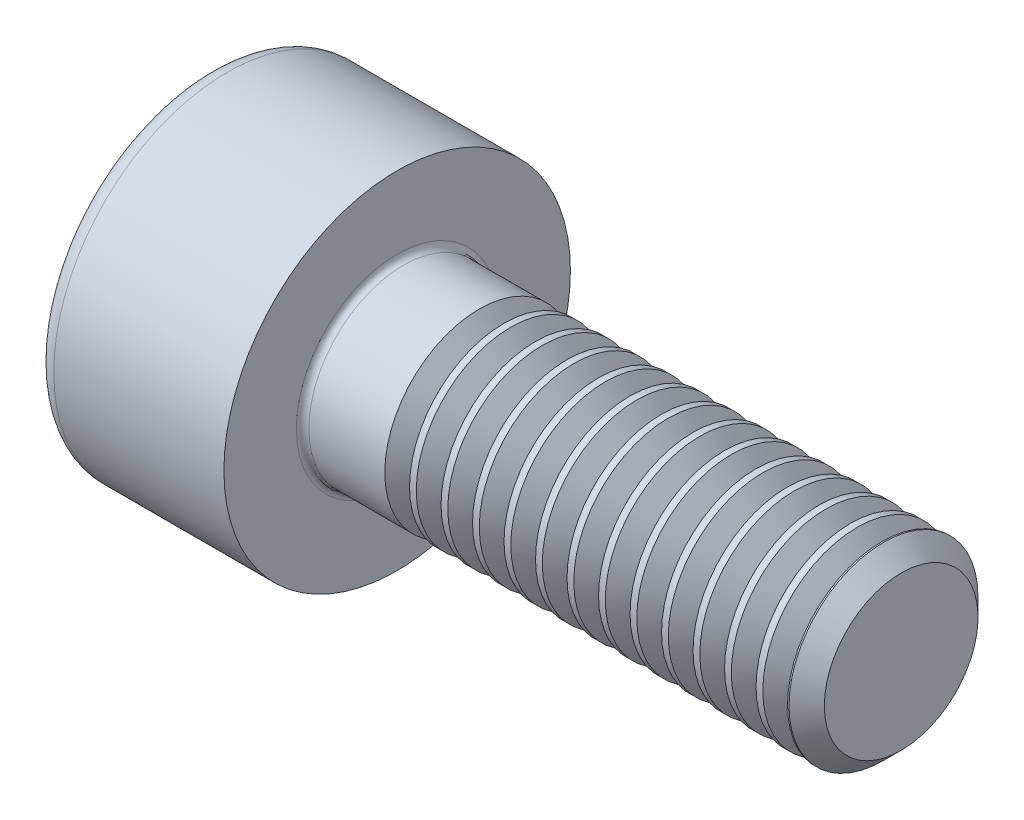
SolidWorks part; units mm, degrees
revolve "Base-Revolve" add sketch "BodySke"
sketch "BodySke" plane through (0, 0, 0) normal (0, 0, 1) x (1, 0, 0)
  line L0 (0, 0) -> (0, 2.75)
  line L1 (0, 2.75) -> (3, 2.75)
  line L2 (3, 2.75) -> (3, 1.5)
  line L3 (3, 1.5) -> (10.7195, 1.5)
  line L4 (11, 1.2195) -> (11, 0)
  line L5 (11, 0) -> (0, 0)
  line L6 (-31.75, 0) -> (127, 0) construction
  line L8 (11, 1.2195) -> (10.7195, 1.5)
  line L10 (11, -1.2195) -> (10.7195, -1.5) construction
  line L11 (3.5, 9.525) -> (3.5, 3.175) construction
  line L12 (3, 9.525) -> (3, 3.175) construction
  line L13 (3, 9.525) -> (3, 3.175) construction
cosmetic thread "ThreadCosmetic" [suppressed]
fillet "Fillet1" radius 0.1 1 edges at (3, 0, 1.5)
fillet "Fillet2" radius 0.3 1 edges at (0, 0, 2.75)
ref_plane "Plane1" through (0, 0, 0) normal (0, 0, 1) x (1, 0, 0)
ref_plane "Plane2" through (0, 0, 0) normal (0, 1, 0) x (1, 0, 0)
ref_plane "Plane3" through (0, 0, 0) normal (1, 0, 0) x (0, 0, -1)
sketch "Sketch2" plane through (0, 0, 0) normal (0, 0, 1) x (1, 0, 0)
  line L0 (0, 1.26) -> (1.3, 1.26)
  line L1 (1.3, 1.26) -> (2.0275, 0)
  line L2 (-31.75, 0) -> (127, 0) construction
  line L3 (2.0275, 0) -> (0, 0)
  line L4 (0, 0) -> (0, 1.26)
  line L6 (0, 0) -> (47.625, 0) construction
revolve "Hex-PreBroach" cut sketch "Sketch2" angle 360 about L6
sketch "Sketch3" plane through (0, 0, 0) normal (-1, 0, 0) x (0, 0.5, 0.866)
  line L0 (0.7275, 1.26) -> (-0.7275, 1.26)
  line L1 (-0.7275, 1.26) -> (-1.4549, 0)
  line L2 (0.7275, 1.26) -> (1.4549, 0)
  line L3 (0.7275, -1.26) -> (1.4549, 0)
  line L4 (0.7275, -1.26) -> (-0.7275, -1.26)
  line L5 (-0.7275, -1.26) -> (-1.4549, 0)
extrude "Hex" cut sketch "Sketch3" against normal blind 1.3
sketch "ThdSchSke" plane through (0, 0, 0) normal (0, 0, 1) x (1, 0, 0)
  line L0 (4.5, -1.2195) -> (4.3036, -1.5)
  line L1 (4.5, -1.2195) -> (4.6964, -1.5)
  line L2 (4.6964, -1.5) -> (4.6964, -1.875)
  line L3 (-3.175, 0) -> (5.1513, 0) construction
  line L4 (0, 2.45) -> (0, -2.45) construction
  line L5 (4.6964, -1.875) -> (4.3036, -1.875)
  line L6 (4.3036, -1.875) -> (4.3036, -1.5)
revolve "ThreadSchematic" cut sketch "ThdSchSke" angle 360 about L3
pattern_linear "ThdSchPat" count 13 spacing 0.5 along (1, 0, 0) of "ThreadSchematic"
equation "\"D2@Sketch3\" = \"Hex_size@Sketch3\" / 2"
equation "\"D1@Sketch3\" = \"Hex_size@Sketch3\" / 2"
equation "\"D1@Sketch2\" = \"Hex_size@Sketch3\" / 2"
equation "\"Thread_minor@ThreadCosmetic\"  =  \"Minor_dia@BodySke\""
equation "\"Depth@Sketch2\" =  \"Key_eng@Hex\""
equation "\"Thread_length@ThreadCosmetic\" = ((sgn( (\"Length@BodySke\" - \"Advance@BodySke\" * 3.0) - \"Thread_nom@BodySke\" )-1)*( (\"Length@BodySke\" - \"Advance@BodySke\" * 3.0) - \"Thread_nom@BodySke\" ))/-2+ \"Thread_nom@BodySke\""
equation "\"Thread_minor@ThdSchSke\" = \"Minor_dia@BodySke\""
equation "\"Diameter@ThdSchSke\" = \"Diameter@BodySke\""
equation "\"Overcut@ThdSchSke\" = \"Diameter@BodySke\" * 1.25"
equation "\"Start@ThdSchSke\" = \"Head_ht@BodySke\" + \"Length@BodySke\" - \"Thread_length@ThreadCosmetic\"  '---Non-countersunk---"
equation "\"Num_threads@ThdSchPat\" = int( \"Thread_length@ThreadCosmetic\" / \"Advance@BodySke\" + 0.999 )  + 1"
equation "\"Advance@ThdSchPat\" = \"Thread_length@ThreadCosmetic\" /  (\"Num_threads@ThdSchPat\" - 1) 'relax it"
equation "\"Num_threads@ThdSchPat\" = \"Num_threads@ThdSchPat\" - sgn( \"Num_threads@ThdSchPat\" - 1) '---chamfered tips only---"
